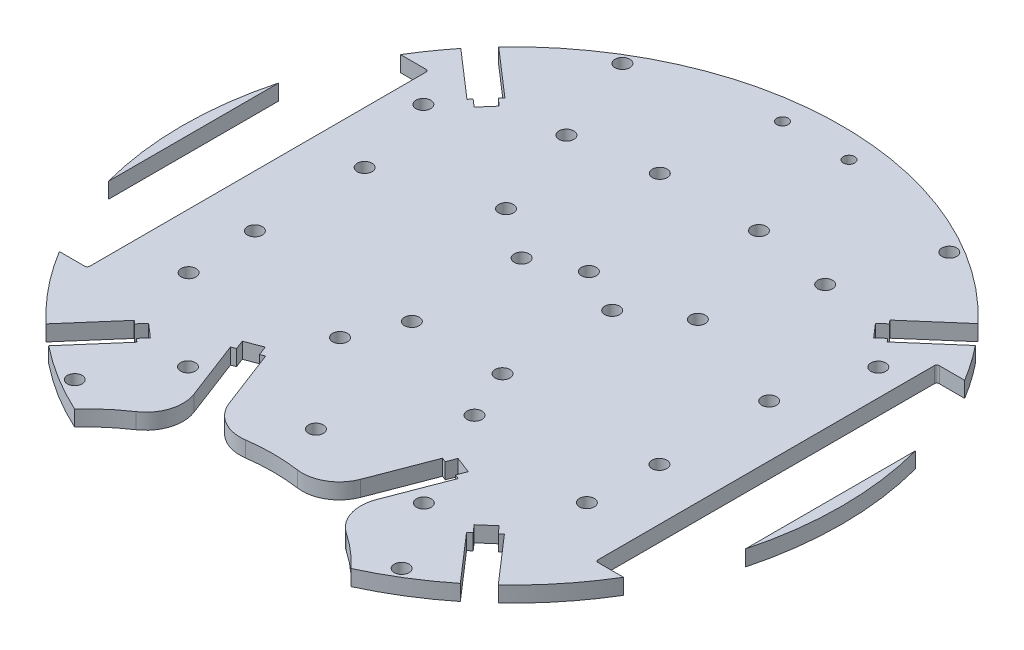
SolidWorks part; units mm, degrees
ref_plane "Front Plane" through (0, 0, 0) normal (0, 0, 1) x (1, 0, 0)
ref_plane "Top Plane" through (0, 0, 0) normal (0, 1, 0) x (1, 0, 0)
ref_plane "Right Plane" through (0, 0, 0) normal (1, 0, 0) x (0, 0, -1)
sketch "Sketch1" plane through (0, 0, 0) normal (0, 1, 0) x (1, 0, 0)
  line L0 (0, 0) -> (-51.5062, -59.2511) construction
  line L1 (0, 86.2583) -> (0, -96.8543) construction
  line L2 (-26.1633, 37.1696) -> (-32.2721, 24.2954) construction
  line L3 (-32.9956, -67.352) -> (0, -86.402) construction
  line L4 (32.9956, -67.352) -> (0, -86.402) construction
  line L5 (0, 0) -> (-13.6167, -50.8184) construction
  line L6 (-33.3347, -42.5389) -> (-41.6896, -52.1501)
  line L7 (-32.2721, 24.2954) -> (-46.0115, 28.0759) construction
  line L8 (-83.3992, 0) -> (107.0959, 0) construction
  line L9 (51.4101, -34) -> (51.4101, 34)
  line L10 (-63.9101, -34.5) -> (-51.9101, -34.5)
  line L11 (-64.4101, -34) -> (-64.4101, 34)
  line L12 (-63.9101, 34.5) -> (-51.9101, 34.5)
  line L13 (-51.4101, -34) -> (-51.4101, 34)
  line L14 (63.9101, 34.5) -> (51.9101, 34.5)
  line L15 (64.4101, -34) -> (64.4101, 34)
  line L16 (63.9101, -34.5) -> (51.9101, -34.5)
  line L17 (0, 0) -> (13.6167, -50.8184) construction
  line L18 (-33.3347, -42.5389) -> (-37.4364, -38.9734)
  line L19 (0, 0) -> (-95.645, -6.6882) construction
  line L20 (-35.4565, -38.0444) -> (-36.7686, -39.5538)
  line L21 (-42.4961, 33.3839) -> (-52.1073, 41.7388)
  line L22 (33.3347, -42.5389) -> (41.6896, -52.1501)
  line L23 (37.4364, -38.9734) -> (45.7913, -48.5846)
  line L24 (-38.9306, 37.4856) -> (-42.4961, 33.3839)
  line L25 (-38.9306, 37.4856) -> (-48.5418, 45.8405)
  line L26 (33.3347, -42.5389) -> (37.4364, -38.9734)
  line L27 (38.9306, 37.4856) -> (42.4961, 33.3839)
  line L28 (42.4961, 33.3839) -> (52.1073, 41.7388)
  line L29 (-18.4555, -45.8919) -> (-23.0382, -33.9163)
  line L30 (-23.0382, -33.9163) -> (-17.8856, -31.9446)
  line L31 (38.9306, 37.4856) -> (48.5418, 45.8405)
  line L32 (-57.9101, -34.5) -> (-57.9101, 19.5819) construction
  line L33 (-37.4364, -38.9734) -> (-45.7913, -48.5846)
  line L34 (-35.4565, -38.0444) -> (-32.7396, -40.4062)
  line L35 (-13.6167, -50.8184) -> (-25.0697, -20.8893) construction
  line L36 (-32.7396, -40.4062) -> (-34.0517, -41.9156)
  line L37 (-13.303, -43.9202) -> (-17.8856, -31.9446)
  line L38 (13.6167, -50.8184) -> (24.3327, -22.8079) construction
  line L39 (18.4555, -45.8919) -> (23.0382, -33.9163)
  line L40 (23.0382, -33.9163) -> (17.8856, -31.9446)
  line L41 (13.303, -43.9202) -> (17.8856, -31.9446)
  line L42 (-58.5537, 0) -> (91.2411, 0) construction
  line L43 (-40.4062, 32.7396) -> (-41.9156, 34.0517)
  line L44 (-38.0444, 35.4565) -> (-39.5538, 36.7686)
  line L45 (-40.4062, 32.7396) -> (-38.0444, 35.4565)
  line L46 (0, 34.6626) -> (0, -51.647) construction
  line L47 (-37.1849, 0) -> (48.113, 0) construction
  line L48 (0, 49.2959) -> (0, -33.0158) construction
  line L49 (40.4062, 32.7396) -> (41.9156, 34.0517)
  line L50 (40.4062, 32.7396) -> (38.0444, 35.4565)
  line L51 (38.0444, 35.4565) -> (39.5538, 36.7686)
  line L52 (35.4565, -38.0444) -> (36.7686, -39.5538)
  line L53 (32.7396, -40.4062) -> (34.0517, -41.9156)
  line L54 (35.4565, -38.0444) -> (32.7396, -40.4062)
  line L55 (-22.143, -33.5738) -> (-22.8578, -31.7059)
  line L56 (-18.7808, -32.2872) -> (-19.4956, -30.4193)
  line L57 (-22.8578, -31.7059) -> (-19.4956, -30.4193)
  line L58 (22.143, -33.5738) -> (22.8578, -31.7059)
  line L59 (22.8578, -31.7059) -> (19.4956, -30.4193)
  line L60 (18.7808, -32.2872) -> (19.4956, -30.4193)
  arc A0 (35.4973, -66.0677) -> (-35.4973, -66.0677) centre (0, 0) ccw
  arc A1 (31.59, -65.1022) -> (-31.59, -65.1022) centre (0, -86.402) ccw
  circle A2 centre (0, 0) radius 74 construction
  circle A3 centre (-13.6089, -21.1831) radius 1.5
  circle A4 centre (27.6453, -18.6148) radius 14.218 construction
  arc A5 (40.0385, -63.4186) -> (41.6896, -52.1501) centre (36.0347, -57.0767) ccw
  arc A6 (57.2158, -48.4905) -> (45.7913, -48.5846) centre (51.4635, -43.6779) cw
  circle A7 centre (27.6453, -18.6148) radius 12.095 construction
  circle A8 centre (-46.0115, 28.0759) radius 1.5
  circle A9 centre (13.6089, -21.1831) radius 1.5
  circle A10 centre (23.8525, -41.6946) radius 1.5
  arc A11 (-57.2158, -48.4905) -> (-45.7913, -48.5846) centre (-51.4635, -43.6779) ccw
  arc A12 (-40.0385, -63.4186) -> (-41.6896, -52.1501) centre (-36.0347, -57.0767) cw
  arc A13 (-5.2626, -48.6672) -> (-13.303, -43.9202) centre (-6.2985, -41.2391) cw
  arc A14 (-21.2728, -54.7938) -> (-18.4555, -45.8919) centre (-25.4604, -48.5717) ccw
  circle A15 centre (-26.2497, -27.6477) radius 12.095 construction
  circle A16 centre (-26.2497, -27.6477) radius 14.25 construction
  arc A17 (21.2728, -54.7938) -> (18.4555, -45.8919) centre (25.4604, -48.5717) cw
  arc A18 (5.2626, -48.6672) -> (13.303, -43.9202) centre (6.2985, -41.2391) ccw
  circle A19 centre (-40.9101, 11.1) radius 1.5
  circle A20 centre (-40.9101, -11.1) radius 1.5
  circle A21 centre (-9.1601, -11.1) radius 1.5
  circle A22 centre (-9.1601, 11.1) radius 1.5
  circle A23 centre (9.1601, 11.1) radius 1.5
  circle A24 centre (9.1601, -11.1) radius 1.5
  circle A25 centre (40.9101, -11.1) radius 1.5
  circle A26 centre (40.9101, 11.1) radius 1.5
  circle A27 centre (-23.8525, -41.6946) radius 1.5
  circle A28 centre (19.3979, 18.1866) radius 1.5
  circle A29 centre (0, 29.7936) radius 12.095 construction
  circle A30 centre (0, -25.4092) radius 12.095 construction
  circle A31 centre (-40.2774, -25.1402) radius 1.5
  circle A32 centre (40.2774, -25.1402) radius 1.5
  circle A33 centre (6.731, 61.4226) radius 1.143
  circle A34 centre (-6.731, 61.4226) radius 1.143
  arc A35 (-5.8539, 64.7449) -> (5.8576, 64.7385) centre (0, 61.4226) cw construction
  arc A36 (5.8576, 64.7385) -> (5.8576, 58.1067) centre (6.731, 61.4226) cw construction
  arc A37 (-5.8539, 58.1002) -> (-5.8539, 64.7449) centre (-6.731, 61.4226) cw construction
  arc A38 (5.8576, 58.1067) -> (-5.8539, 58.1002) centre (0, 61.4226) cw construction
  circle A39 centre (26.2497, -27.6477) radius 14.25 construction
  circle A42 centre (32.2721, 24.2954) radius 14.25 construction
  circle A43 centre (-32.2721, 24.2954) radius 12.095 construction
  circle A44 centre (26.1633, 37.1696) radius 1.5
  circle A45 centre (32.2721, 24.2954) radius 12.095 construction
  circle A46 centre (-27.6453, -18.6148) radius 12.095 construction
  circle A47 centre (26.2497, -27.6477) radius 12.095 construction
  circle A48 centre (46.0115, 28.0759) radius 1.5
  circle A49 centre (-20.0544, 50.0438) radius 12.095 construction
  circle A50 centre (10.0272, 39.9187) radius 1.5
  arc A51 (-35.4973, -66.0677) -> (-31.59, -65.1022) centre (-34.0774, -63.425) ccw
  arc A52 (35.4973, -66.0677) -> (31.59, -65.1022) centre (34.0774, -63.425) cw
  circle A53 centre (0, -39.6592) radius 1.5
  circle A54 centre (-32.2721, 24.2954) radius 14.25 construction
  circle A55 centre (-10.0272, 39.9187) radius 1.5
  circle A56 centre (20.0544, 50.0438) radius 14.25 construction
  circle A57 centre (20.0544, 50.0438) radius 12.095 construction
  circle A58 centre (0, 29.7936) radius 14.25 construction
  circle A59 centre (-33.0597, -55.3832) radius 1.5
  circle A60 centre (-33.0597, 55.3832) radius 1.5
  circle A61 centre (33.0597, -55.3832) radius 1.5
  circle A62 centre (0, 15.5436) radius 1.5
  circle A63 centre (-26.1633, 37.1696) radius 1.5
  circle A64 centre (0, 0) radius 64.5 construction
  circle A65 centre (-19.3979, 18.1866) radius 1.5
  circle A66 centre (-20.0544, 50.0438) radius 14.25 construction
  circle A67 centre (33.0597, 55.3832) radius 1.5
  arc A68 (-48.475, 57.2291) -> (-48.5418, 45.8405) centre (-43.6275, 51.5062) ccw
  arc A69 (-63.4075, 40.0557) -> (-52.1073, 41.7388) centre (-57.0415, 36.0905) cw
  arc A70 (63.4075, 40.0557) -> (52.1073, 41.7388) centre (57.0415, 36.0905) ccw
  arc A71 (48.475, 57.2291) -> (48.5418, 45.8405) centre (43.6275, 51.5062) cw
  arc A72 (-64.4101, -34) -> (-63.9101, -34.5) centre (-63.9101, -34) ccw
  arc A73 (-51.4101, -34) -> (-51.9101, -34.5) centre (-51.9101, -34) cw
  circle A74 centre (-27.6453, -18.6148) radius 14.218 construction
  arc A75 (-51.4101, 34) -> (-51.9101, 34.5) centre (-51.9101, 34) ccw
  arc A76 (-64.4101, 34) -> (-63.9101, 34.5) centre (-63.9101, 34) cw
  arc A77 (64.4101, 34) -> (63.9101, 34.5) centre (63.9101, 34) ccw
  circle A78 centre (0, -25.4092) radius 14.25 construction
  arc A79 (51.4101, 34) -> (51.9101, 34.5) centre (51.9101, 34) cw
  arc A80 (51.4101, -34) -> (51.9101, -34.5) centre (51.9101, -34) ccw
  arc A81 (64.4101, -34) -> (63.9101, -34.5) centre (63.9101, -34) cw
  point P14 (-62.6039, 0)
  point P23 (62.6039, 0)
  point P35 (-31.5178, -45.012)
  point P40 (-46.7211, -26.9744)
  point P45 (-23.8153, 50.3782)
  point P48 (0, -25.4092)
  point P84 (-20.4619, -32.9305)
  point P154 (0, 58.1002)
  dimension "D1" = 150
  dimension "D2" = 76.2
  dimension "D10" = 148
  dimension "D13" = 3
  dimension "D14" = 3
  dimension "D22" = 2.286
  dimension "D20" = 3
  dimension "D11" = 24.19
  dimension "D12" = 28.436
  dimension "D24" = 28.5
  dimension "D21" = 24.19
  dimension "D25" = 28.5
  dimension "D26" = 28.5
  dimension "D29" = 28.5
  dimension "D8" = 28.5
  dimension "D16" = 6
  dimension "D3" = 120
  dimension "D9" = 30
  dimension "D6" = 12.8224
  dimension "D17" = 22.2
  dimension "D19" = 22.2
  dimension "D15" = 10.5
  dimension "D18" = 31.75
  dimension "D23" = 13.462
  dimension "D31" = 100
  dimension "D27" = 45
  dimension "D28" = 12.735
  dimension "D4" = 3.6
  dimension "D5" = 2
  dimension "D7" = 2
  dimension "D32" = 1.8
  dimension "D33" = 13
  dimension "D30" = 170
extrude "Boss-Extrude1" add sketch "Sketch1" along normal blind 3.175
sketch "Sketch2" plane through (0, 3.175, 0) normal (0, 1, 0) x (1, 0, 0)
  circle A0 centre (0, 0) radius 66.67
  circle A1 centre (0, 0) radius 80.936
extrude "Cut-Extrude1" cut sketch "Sketch2" against normal blind 10
equation "\"D10@Sketch1\"=150-2"
